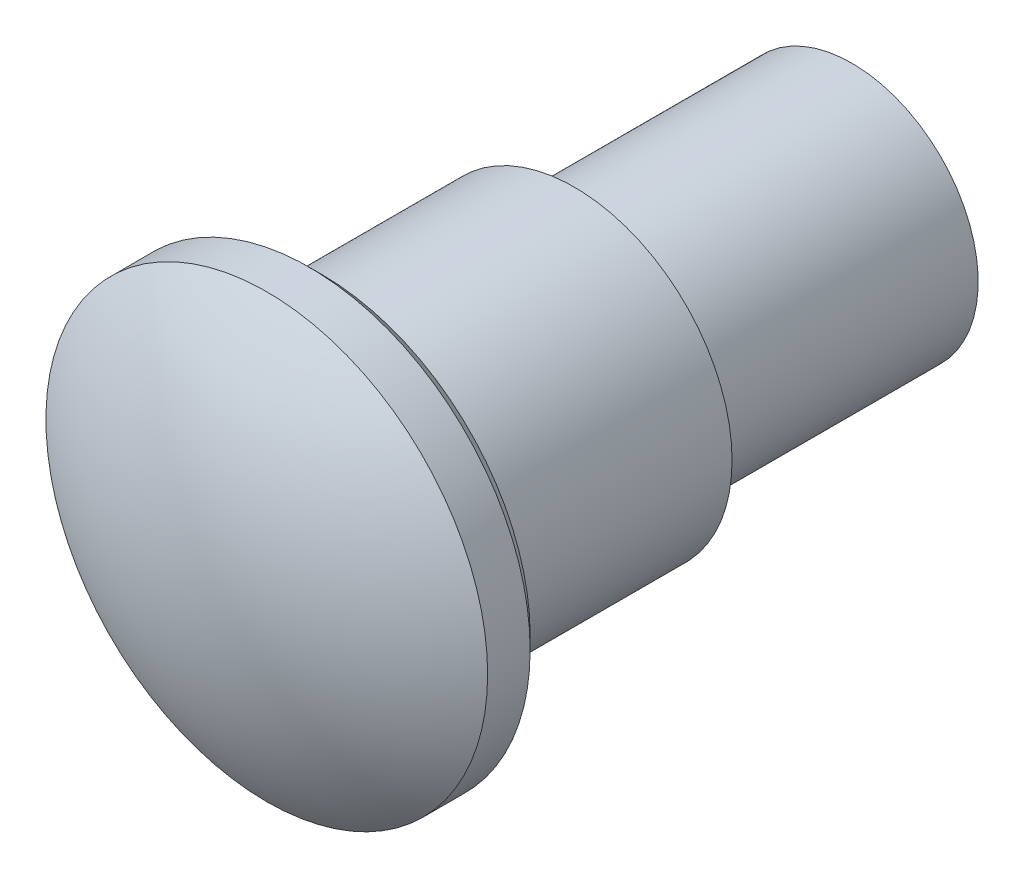
SolidWorks part; units mm, degrees
ref_plane "Front Plane" through (0, 0, 0) normal (0, 0, 1) x (1, 0, 0)
ref_plane "Top Plane" through (0, 0, 0) normal (0, 1, 0) x (1, 0, 0)
ref_plane "Right Plane" through (0, 0, 0) normal (1, 0, 0) x (0, 0, -1)
sketch "Sketch2" plane through (0, 0, 0) normal (0, 0, 1) x (1, 0, 0)
  circle A0 centre (0, 0) radius 1.75
  dimension "D1" = 3.5
extrude "Boss-Extrude1" add sketch "Sketch2" against normal blind 5.2
sketch "Sketch3" plane through (0, 0, 0) normal (1, 0, 0) x (0, 0, -1)
  line L0 (5.2, 1.75) -> (0, 1.75) construction
  line L1 (0, 1.75) -> (0, -1.75) construction
  line L3 (0, 0) -> (-0.5, 0)
  line L4 (-0.5, 1.75) -> (-0.5, -1.75)
  line L5 (-0.5, 1.75) -> (-0.5, 0)
  line L6 (0.5633, 1.75) -> (-0.5, 1.75)
  line L7 (0, 0) -> (5.2, 0) construction
  line L8 (5.2, -1.75) -> (5.2, 1.75) construction
  arc A0 (0, 0) -> (0.5633, 1.75) centre (3, 0) cw
  dimension "D1" = 3
  dimension "D2" = 0.5
revolve "Cut-Revolve1" cut sketch "Sketch3" angle 360 about L7
sketch "Sketch4" plane through (0, 0, -5.2) normal (0, 0, -1) x (-1, 0, 0)
  circle A0 centre (0, 0) radius 1
  dimension "D1" = 2
extrude "Cut-Extrude1" cut sketch "Sketch4" against normal blind 2.2 flip side to cut contours A0
sketch "Sketch5" plane through (0, 0, -3) normal (0, 0, -1) x (-1, 0, 0)
  circle A0 centre (0, 0) radius 1.25
  dimension "D1" = 2.5
extrude "Cut-Extrude2" cut sketch "Sketch5" against normal blind 2 flip side to cut
chamfer "Chamfer1" distance 0.1 angle 45 1 edges at (-1.75, 0, -1)
sketch "Sketch6" plane through (0, 0, 0) normal (1, 0, 0) x (0, 0, -1)
  line L0 (0, 0) -> (5.2, 0) construction
  line L1 (5.2, -1) -> (5.2, 1) construction
  line L2 (5.2, 0.8) -> (4.4, 0)
  line L3 (4.4, 0) -> (5.2, -0.8) construction
  line L4 (4.4, 0) -> (5.2, 0)
  line L5 (5.2, 0) -> (5.2, 0.8)
  dimension "D1" = 1.6
revolve "Cut-Revolve2" cut sketch "Sketch6" angle 360 about L0
